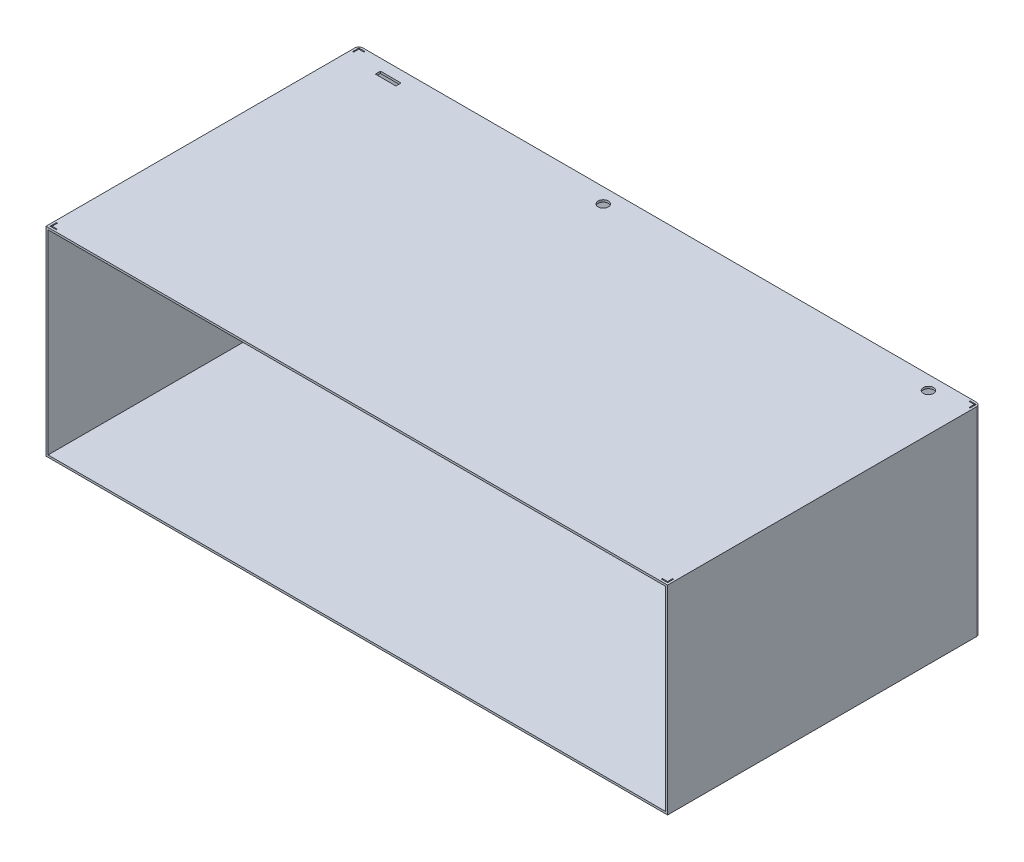
SolidWorks part; units mm, degrees
material "PVC Rigid"
ref_plane "Front Plane" through (0, 0, 0) normal (0, 0, 1) x (1, 0, 0)
ref_plane "Top Plane" through (0, 0, 0) normal (0, 1, 0) x (1, 0, 0)
ref_plane "Right Plane" through (0, 0, 0) normal (1, 0, 0) x (0, 0, -1)
sketch "Sketch1" plane through (0, 0, 0) normal (0, 0, 1) x (1, 0, 0)
  line L1 (-604, 193.5) -> (604, 193.5)
  line L2 (-604, 193.5) -> (-604, -193.5)
  line L3 (-604, -193.5) -> (604, -193.5)
  line L4 (604, 193.5) -> (604, -193.5)
  line L5 (-604, 193.5) -> (604, -193.5) construction
  line L6 (-604, -193.5) -> (604, 193.5) construction
  point P0 (0, 0)
extrude "Boss-Extrude1" add sketch "Sketch1" along normal blind 608
sketch "Sketch2" plane through (0, 0, 608) normal (0, 0, 1) x (1, 0, 0)
  line L1 (-600, 189.5) -> (600, 189.5)
  line L2 (-600, 189.5) -> (-600, -189.5)
  line L3 (-600, -189.5) -> (600, -189.5)
  line L4 (600, 189.5) -> (600, -189.5)
  line L5 (-600, 189.5) -> (600, -189.5) construction
  line L6 (-600, -189.5) -> (600, 189.5) construction
  point P0 (0, 0)
extrude "Cut-Extrude1" cut sketch "Sketch2" against normal blind 604 contours L1 L4 L3 L2
sketch "Sketch3" plane through (0, -193.5, 0) normal (0, -1, 0) x (1, 0, 0)
  line L0 (-604, 608) -> (604, 608) construction
  line L1 (-604, 608) -> (-604, 0) construction
  line L2 (604, 608) -> (604, 0) construction
  line L3 (-604, 0) -> (604, 0) construction
  circle A0 centre (-504, 528) radius 25 construction
  circle A1 centre (504, 528) radius 25 construction
  circle A2 centre (-504, 80) radius 25 construction
  circle A3 centre (504, 80) radius 25 construction
  dimension "D1" = 80
  dimension "D3" = 100
  dimension "D5" = 80
  dimension "D2" = 100
  dimension "D4" = 80
fillet "Fillet1" radius 8 2 edges at (-604, 0, 0) (604, 0, 0)
sketch "Sketch4" plane through (0, 193.5, 0) normal (0, 1, 0) x (1, 0, 0)
  line L0 (-604, -608) -> (-604, -8) construction
  line L1 (604, -608) -> (-604, -608) construction
  line L2 (-600, -604) -> (-588, -604)
  line L3 (-588, -604) -> (-588, -602)
  line L4 (-588, -602) -> (-598, -602)
  line L5 (-598, -602) -> (-598, -592)
  line L6 (-598, -592) -> (-600, -592)
  line L7 (-600, -592) -> (-600, -604)
  point P0 (-600, -604)
  dimension "D1" = 4
  dimension "D2" = 4
extrude "Cut-Extrude2" cut sketch "Sketch4" against normal blind 2
mirror "Mirror1" about plane through (0, 0, 0) normal (1, 0, 0) of "Cut-Extrude2"
ref_plane "Plane1" through (0, 0, 304) normal (0, 0, 1) x (1, 0, 0)
mirror "Mirror2" about plane through (0, 0, 304) normal (0, 0, 1) of "Mirror1", "Cut-Extrude2"
sketch "Sketch5" plane through (0, 193.5, 0) normal (0, 1, 0) x (1, 0, 0)
  line L0 (596, 0) -> (-596, 0) construction
  line L1 (-500, -22) -> (-540, -22)
  line L2 (-500, -22) -> (-500, -32)
  line L3 (-500, -32) -> (-540, -32)
  line L4 (-540, -22) -> (-540, -32)
  line L5 (-500, -22) -> (-540, -32) construction
  line L6 (-500, -32) -> (-540, -22) construction
  line L8 (-604, -608) -> (-604, -8) construction
  circle A0 centre (-100, -29) radius 10
  circle A1 centre (530, -27) radius 10
  point P0 (-520, -27)
  dimension "D3" = 29
  dimension "D5" = 27
  dimension "D1" = 22
  dimension "D2" = 64
  dimension "D4" = 504
  dimension "D6" = 1134
extrude "Cut-Extrude4" cut sketch "Sketch5" against normal up to surface (4 mm away) up to face at (0, 189.5, 306)
